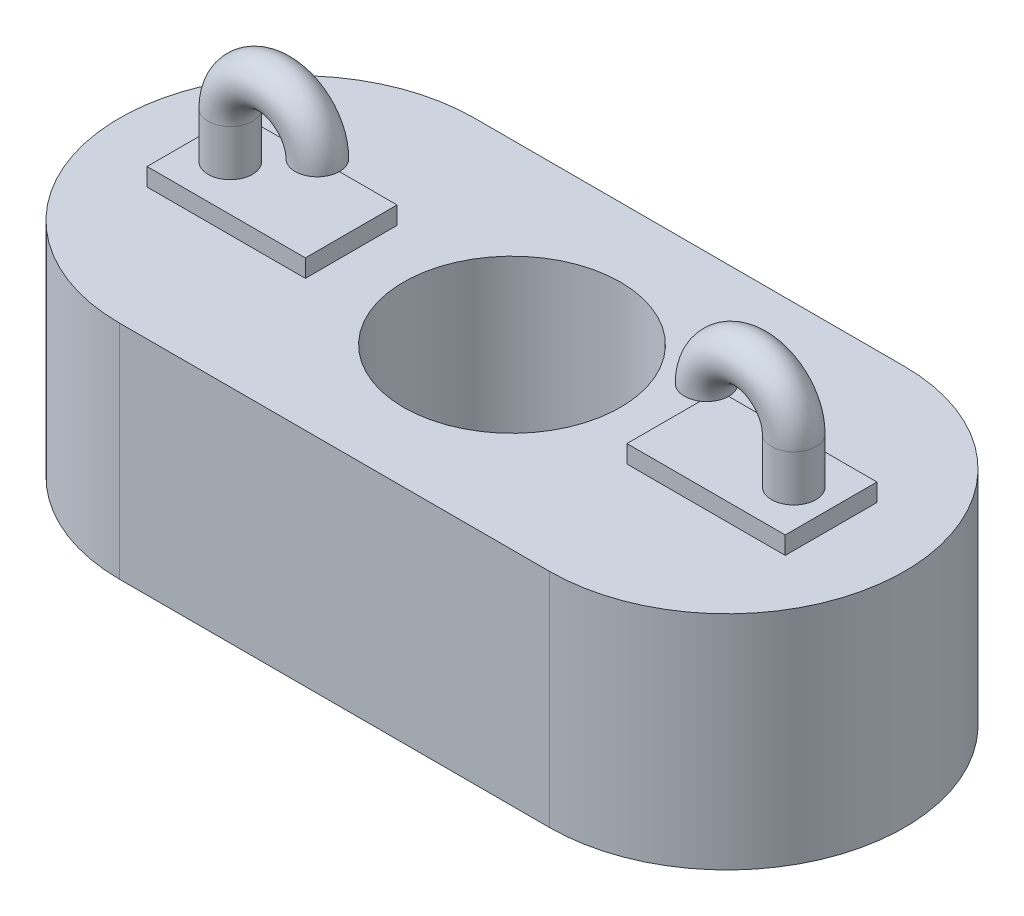
SolidWorks part; units mm, degrees
ref_plane "Front Plane" through (0, 0, 0) normal (0, 0, 1) x (1, 0, 0)
ref_plane "Top Plane" through (0, 0, 0) normal (0, 1, 0) x (1, 0, 0)
ref_plane "Right Plane" through (0, 0, 0) normal (1, 0, 0) x (0, 0, -1)
sketch "Sketch1" plane through (0, 0, 0) normal (0, 1, 0) x (1, 0, 0)
  line L1 (-4.8461, 4) -> (4.8461, 4)
  line L2 (-4.8461, -4) -> (4.8461, -4)
  circle A0 centre (0, 0) radius 2.4454
  arc A1 (-4.8461, 4) -> (-4.8461, -4) centre (-4.8461, 0) ccw
  arc A2 (4.8461, 4) -> (4.8461, -4) centre (4.8461, 0) cw
  point P6 (0, 0)
  point P9 (0, 4)
  point P12 (0, -4)
extrude "Boss-Extrude1" add sketch "Sketch1" along normal blind 5
sketch "Sketch2" plane through (0, 5, 0) normal (0, 1, 0) x (1, 0, 0)
  line L1 (-7.1907, -1.0333) -> (-3.6236, -1.0333)
  line L2 (-7.1907, -1.0333) -> (-7.1907, 1.0333)
  line L3 (-7.1907, 1.0333) -> (-3.6236, 1.0333)
  line L4 (-3.6236, -1.0333) -> (-3.6236, 1.0333)
  line L5 (-7.1907, -1.0333) -> (-3.6236, 1.0333) construction
  line L6 (-7.1907, 1.0333) -> (-3.6236, -1.0333) construction
  point P0 (-5.4072, 0)
extrude "Boss-Extrude2" add sketch "Sketch2" along normal blind 0.4
sketch "Sketch3" plane through (0, 0, 0) normal (0, 0, 1) x (1, 0, 0)
  line L1 (-6.3486, 5.4) -> (-6.3486, 6.437)
  arc A0 (-6.3486, 6.437) -> (-4.386, 6.437) centre (-5.3673, 6.437) cw
sweep "Sweep2" add path "Sketch3" circular profile diameter 1 parameters "D3"=1
mirror "Mirror1" about plane through (0, 0, 0) normal (1, 0, 0) of "Boss-Extrude2", "Sweep2"
